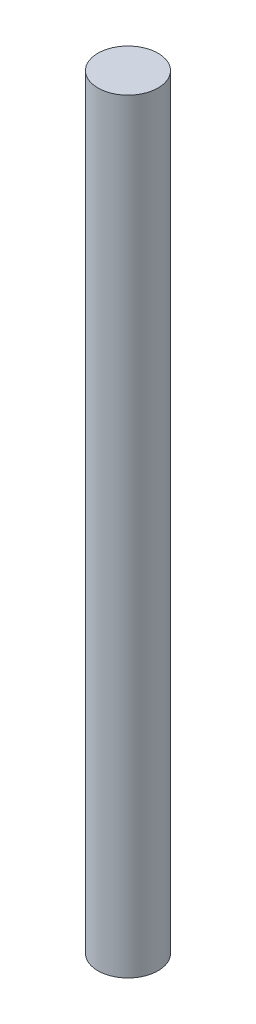
SolidWorks part; units mm, degrees
ref_plane "Front Plane" through (0, 0, 0) normal (0, 0, 1) x (1, 0, 0)
ref_plane "Top Plane" through (0, 0, 0) normal (0, 1, 0) x (1, 0, 0)
ref_plane "Right Plane" through (0, 0, 0) normal (1, 0, 0) x (0, 0, -1)
sketch "Sketch2" plane through (0, 0, 0) normal (0, 1, 0) x (1, 0, 0)
  circle A0 centre (0, 0) radius 1.5
  dimension "D1" = 3
extrude "Boss-Extrude1" add sketch "Sketch2" along normal blind 38.1
